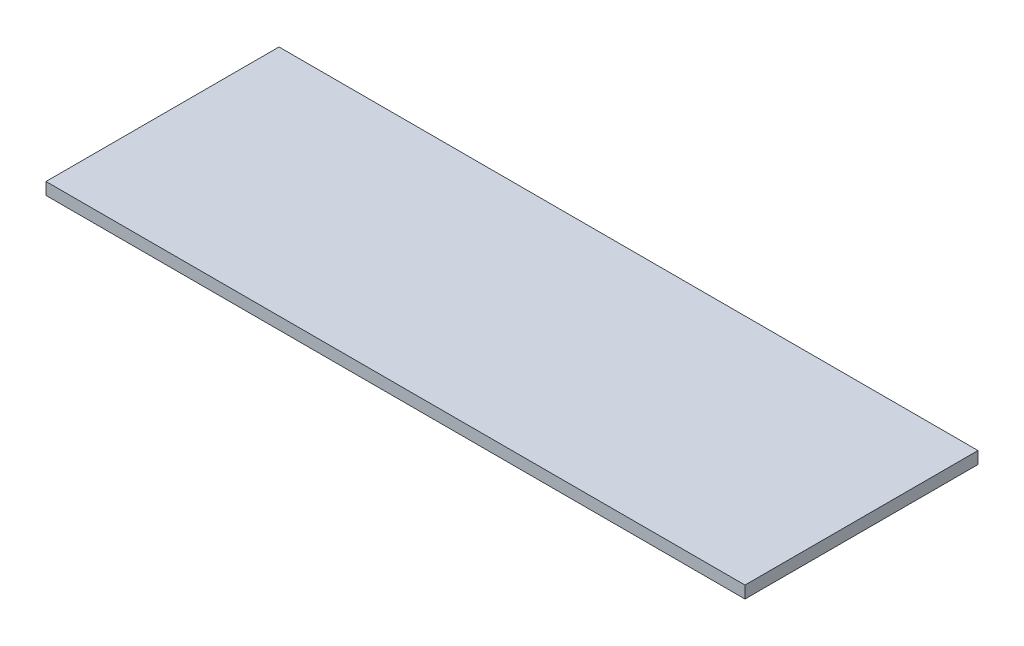
SolidWorks part; units mm, degrees
material "Cedar"
ref_plane "Front Plane" through (0, 0, 0) normal (0, 0, 1) x (1, 0, 0)
ref_plane "Top Plane" through (0, 0, 0) normal (0, 1, 0) x (1, 0, 0)
ref_plane "Right Plane" through (0, 0, 0) normal (1, 0, 0) x (0, 0, -1)
sketch "Sketch1" plane through (0, 0, 0) normal (0, 1, 0) x (1, 0, 0)
  line L1 (-914.4, -304.8) -> (914.4, -304.8)
  line L2 (-914.4, -304.8) -> (-914.4, 304.8)
  line L3 (-914.4, 304.8) -> (914.4, 304.8)
  line L4 (914.4, -304.8) -> (914.4, 304.8)
  line L5 (-914.4, -304.8) -> (914.4, 304.8) construction
  line L6 (-914.4, 304.8) -> (914.4, -304.8) construction
  point P0 (0, 0)
  dimension "D1" = 1828.8
  dimension "D2" = 609.6
extrude "Boss-Extrude1" add sketch "Sketch1" along normal blind 31.75
